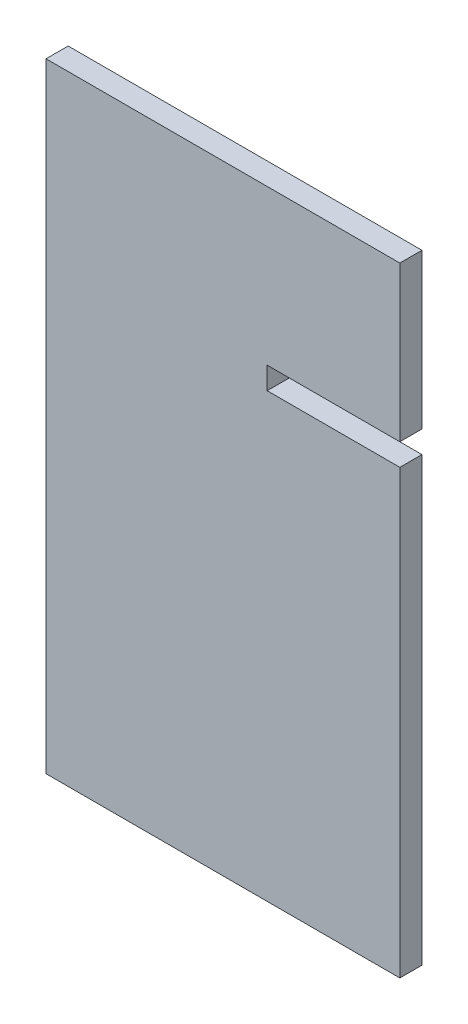
SolidWorks part; units mm, degrees
ref_plane "Plan de face" through (0, 0, 0) normal (0, 0, 1) x (1, 0, 0)
ref_plane "Plan de dessus" through (0, 0, 0) normal (0, 1, 0) x (1, 0, 0)
ref_plane "Plan de droite" through (0, 0, 0) normal (1, 0, 0) x (0, 0, -1)
sketch "Esquisse1" plane through (0, 0, 0) normal (0, 0, 1) x (1, 0, 0)
  line L0 (80, 140) -> (80, 105)
  line L1 (0, 0) -> (80, 0)
  line L2 (0, 0) -> (0, 140)
  line L3 (0, 140) -> (80, 140)
  line L4 (80, 100) -> (80, 0)
  line L5 (50, 105) -> (80, 105)
  line L6 (50, 105) -> (50, 100)
  line L7 (50, 100) -> (80, 100)
  dimension "D1" = 140
  dimension "D2" = 80
  dimension "D3" = 30
  dimension "D4" = 5
  dimension "D5" = 35
extrude "Boss.-Extru.1" add sketch "Esquisse1" along normal blind 5
